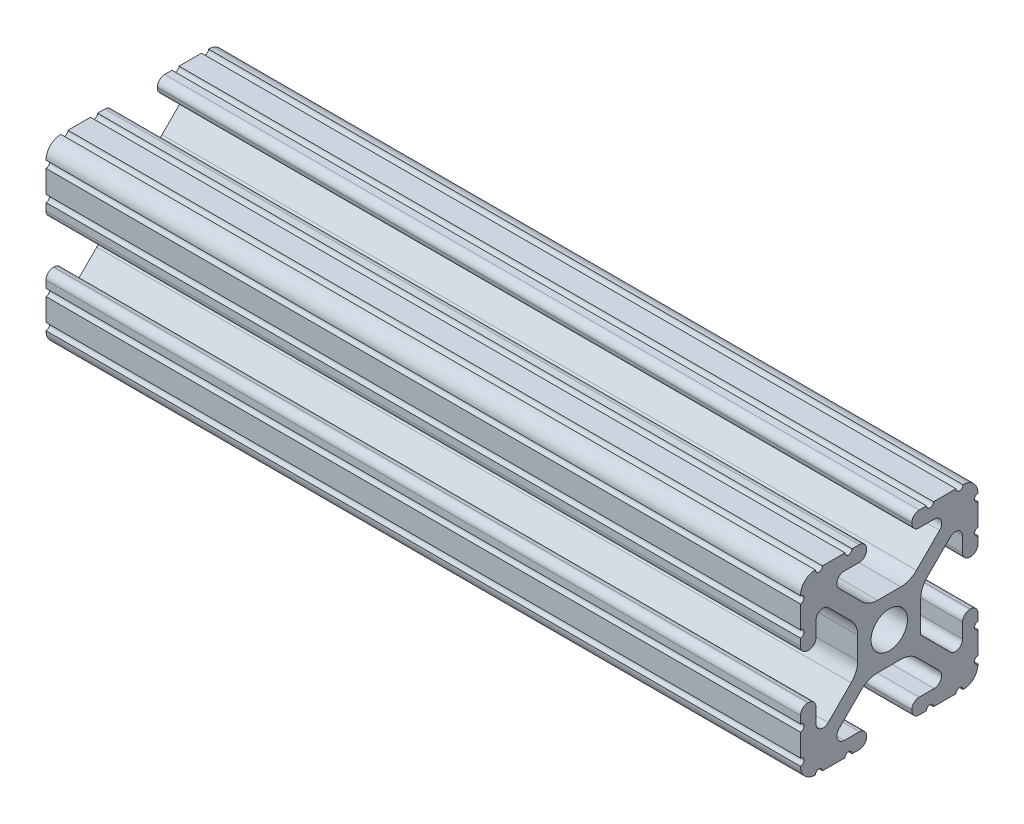
SolidWorks part; units mm, degrees
material "6061-T6 (SS)"
ref_plane "Front Plane" through (0, 0, 0) normal (0, 0, 1) x (1, 0, 0)
ref_plane "Top Plane" through (0, 0, 0) normal (0, 1, 0) x (1, 0, 0)
ref_plane "Right Plane" through (0, 0, 0) normal (1, 0, 0) x (0, 0, -1)
sketch "Sketch1" plane through (0, 0, 0) normal (1, 0, 0) x (0, 0, -1)
  line L0 (6.3331, -12.7) -> (9.5504, -12.7)
  line L1 (12.7, -9.5504) -> (12.7, -6.3331)
  line L2 (12.7, -5.3171) -> (12.7, -4.2875)
  line L3 (11.651, -3.2385) -> (11.5392, -3.2385)
  line L4 (10.4902, -4.2875) -> (10.4902, -6.4021)
  line L5 (8.7371, -7.1294) -> (4.5085, -2.9104)
  line L6 (4.5085, -2.9104) -> (4.5085, 1.5932)
  line L7 (5.441, 3.8408) -> (8.7371, 7.1294)
  line L8 (10.4902, 6.4021) -> (10.4902, 4.2875)
  line L9 (11.5392, 3.2385) -> (11.651, 3.2385)
  line L10 (12.7, 4.2875) -> (12.7, 5.3171)
  line L11 (12.7, 6.3331) -> (12.7, 9.5504)
  line L12 (9.5504, 12.7) -> (6.3331, 12.7)
  line L13 (5.3171, 12.7) -> (4.2875, 12.7)
  line L14 (3.2385, 11.651) -> (3.2385, 11.5392)
  line L15 (4.2875, 10.4902) -> (6.4768, 10.4902)
  line L16 (7.207, 8.7244) -> (3.8983, 5.4232)
  line L17 (1.6558, 4.4958) -> (-1.6558, 4.4958)
  line L18 (-3.8983, 5.4232) -> (-7.207, 8.7244)
  line L19 (-6.4768, 10.4902) -> (-4.2875, 10.4902)
  line L20 (-3.2385, 11.5392) -> (-3.2385, 11.651)
  line L21 (-4.2875, 12.7) -> (-5.3171, 12.7)
  line L22 (-6.3331, 12.7) -> (-9.5504, 12.7)
  line L23 (-12.7, 9.5504) -> (-12.7, 6.3331)
  line L24 (-12.7, 5.3171) -> (-12.7, 4.2875)
  line L25 (-11.651, 3.2385) -> (-11.5392, 3.2385)
  line L26 (-10.4902, 4.2875) -> (-10.4902, 6.4021)
  line L27 (-8.7371, 7.1294) -> (-5.441, 3.8408)
  line L28 (-4.5085, 1.5932) -> (-4.5085, -1.5932)
  line L29 (-5.441, -3.8408) -> (-8.7371, -7.1294)
  line L30 (-10.4902, -6.4021) -> (-10.4902, -4.2875)
  line L31 (-11.5392, -3.2385) -> (-11.651, -3.2385)
  line L32 (-12.7, -4.2875) -> (-12.7, -5.3171)
  line L33 (-12.7, -6.3331) -> (-12.7, -9.5504)
  line L34 (-9.5504, -12.7) -> (-6.3331, -12.7)
  line L35 (-5.3171, -12.7) -> (-4.2875, -12.7)
  line L36 (-3.2385, -11.651) -> (-3.2385, -11.5392)
  line L37 (-4.2875, -10.4902) -> (-6.4164, -10.4902)
  line L38 (-7.1797, -8.6452) -> (-3.9523, -5.4237)
  line L39 (-1.7093, -4.4958) -> (1.7093, -4.4958)
  line L40 (3.9523, -5.4237) -> (7.1797, -8.6452)
  line L41 (6.4164, -10.4902) -> (4.2875, -10.4902)
  line L42 (3.2385, -11.5392) -> (3.2385, -11.651)
  line L43 (4.2875, -12.7) -> (5.3171, -12.7)
  circle A0 centre (0, 0) radius 2.6035
  arc A1 (6.3331, -12.7) -> (5.3171, -12.7) centre (5.8251, -12.7) ccw
  arc A2 (10.5664, -12.6998) -> (9.5504, -12.7) centre (10.0584, -12.7) ccw
  arc A3 (10.5664, -12.6998) -> (12.6998, -10.5664) centre (10.5918, -10.5918) ccw
  arc A4 (12.7, -9.5504) -> (12.6998, -10.5664) centre (12.7, -10.0584) ccw
  arc A5 (12.7, -5.3171) -> (12.7, -6.3331) centre (12.7, -5.8251) ccw
  arc A6 (12.7, -4.2875) -> (11.651, -3.2385) centre (11.651, -4.2875) ccw
  arc A7 (11.5392, -3.2385) -> (10.4902, -4.2875) centre (11.5392, -4.2875) ccw
  arc A8 (8.7371, -7.1294) -> (10.4902, -6.4021) centre (9.4628, -6.4021) ccw
  arc A9 (5.441, 3.8408) -> (4.5085, 1.5932) centre (7.6835, 1.5932) ccw
  arc A10 (10.4902, 6.4021) -> (8.7371, 7.1294) centre (9.4628, 6.4021) ccw
  arc A11 (10.4902, 4.2875) -> (11.5392, 3.2385) centre (11.5392, 4.2875) ccw
  arc A12 (11.651, 3.2385) -> (12.7, 4.2875) centre (11.651, 4.2875) ccw
  arc A13 (12.7, 6.3331) -> (12.7, 5.3171) centre (12.7, 5.8251) ccw
  arc A14 (12.6998, 10.5664) -> (12.7, 9.5504) centre (12.7, 10.0584) ccw
  arc A15 (12.6998, 10.5664) -> (10.5664, 12.6998) centre (10.5918, 10.5918) ccw
  arc A16 (9.5504, 12.7) -> (10.5664, 12.6998) centre (10.0584, 12.7) ccw
  arc A17 (5.3171, 12.7) -> (6.3331, 12.7) centre (5.8251, 12.7) ccw
  arc A18 (4.2875, 12.7) -> (3.2385, 11.651) centre (4.2875, 11.651) ccw
  arc A19 (3.2385, 11.5392) -> (4.2875, 10.4902) centre (4.2875, 11.5392) ccw
  arc A20 (7.207, 8.7244) -> (6.4768, 10.4902) centre (6.4768, 9.4563) ccw
  arc A21 (1.6558, 4.4958) -> (3.8983, 5.4232) centre (1.6558, 7.6708) ccw
  arc A22 (-3.8983, 5.4232) -> (-1.6558, 4.4958) centre (-1.6558, 7.6708) ccw
  arc A23 (-6.4768, 10.4902) -> (-7.207, 8.7244) centre (-6.4768, 9.4563) ccw
  arc A24 (-4.2875, 10.4902) -> (-3.2385, 11.5392) centre (-4.2875, 11.5392) ccw
  arc A25 (-3.2385, 11.651) -> (-4.2875, 12.7) centre (-4.2875, 11.651) ccw
  arc A26 (-6.3331, 12.7) -> (-5.3171, 12.7) centre (-5.8251, 12.7) ccw
  arc A27 (-10.5664, 12.6998) -> (-9.5504, 12.7) centre (-10.0584, 12.7) ccw
  arc A28 (-10.5664, 12.6998) -> (-12.6998, 10.5664) centre (-10.5918, 10.5918) ccw
  arc A29 (-12.7, 9.5504) -> (-12.6998, 10.5664) centre (-12.7, 10.0584) ccw
  arc A30 (-12.7, 5.3171) -> (-12.7, 6.3331) centre (-12.7, 5.8251) ccw
  arc A31 (-12.7, 4.2875) -> (-11.651, 3.2385) centre (-11.651, 4.2875) ccw
  arc A32 (-11.5392, 3.2385) -> (-10.4902, 4.2875) centre (-11.5392, 4.2875) ccw
  arc A33 (-8.7371, 7.1294) -> (-10.4902, 6.4021) centre (-9.4628, 6.4021) ccw
  arc A34 (-4.5085, 1.5932) -> (-5.441, 3.8408) centre (-7.6835, 1.5932) ccw
  arc A35 (-5.441, -3.8408) -> (-4.5085, -1.5932) centre (-7.6835, -1.5932) ccw
  arc A36 (-10.4902, -6.4021) -> (-8.7371, -7.1294) centre (-9.4628, -6.4021) ccw
  arc A37 (-10.4902, -4.2875) -> (-11.5392, -3.2385) centre (-11.5392, -4.2875) ccw
  arc A38 (-11.651, -3.2385) -> (-12.7, -4.2875) centre (-11.651, -4.2875) ccw
  arc A39 (-12.7, -6.3331) -> (-12.7, -5.3171) centre (-12.7, -5.8251) ccw
  arc A40 (-12.6998, -10.5664) -> (-12.7, -9.5504) centre (-12.7, -10.0584) ccw
  arc A41 (-12.6998, -10.5664) -> (-10.5664, -12.6998) centre (-10.5918, -10.5918) ccw
  arc A42 (-9.5504, -12.7) -> (-10.5664, -12.6998) centre (-10.0584, -12.7) ccw
  arc A43 (-5.3171, -12.7) -> (-6.3331, -12.7) centre (-5.8251, -12.7) ccw
  arc A44 (-4.2875, -12.7) -> (-3.2385, -11.651) centre (-4.2875, -11.651) ccw
  arc A45 (-3.2385, -11.5392) -> (-4.2875, -10.4902) centre (-4.2875, -11.5392) ccw
  arc A46 (-7.1797, -8.6452) -> (-6.4164, -10.4902) centre (-6.4164, -9.4098) ccw
  arc A47 (-1.7093, -4.4958) -> (-3.9523, -5.4237) centre (-1.7093, -7.6708) ccw
  arc A48 (3.9523, -5.4237) -> (1.7093, -4.4958) centre (1.7093, -7.6708) ccw
  arc A49 (6.4164, -10.4902) -> (7.1797, -8.6452) centre (6.4164, -9.4098) ccw
  arc A50 (4.2875, -10.4902) -> (3.2385, -11.5392) centre (4.2875, -11.5392) ccw
  arc A51 (3.2385, -11.651) -> (4.2875, -12.7) centre (4.2875, -11.651) ccw
extrude "Boss-Extrude1" add sketch "Sketch1" along normal blind 107.95
sketch "Sketch2" plane through (0, 0, 0) normal (0, 0, 1) x (1, 0, 0)
  circle A0 centre (44.45, 0) radius 3.175
  circle A1 centre (44.45, 0) radius 2.6035 construction
  dimension "D1" = 6.35
extrude "Cut-Extrude1" cut sketch "Sketch2" against normal through all both and the other way through all
